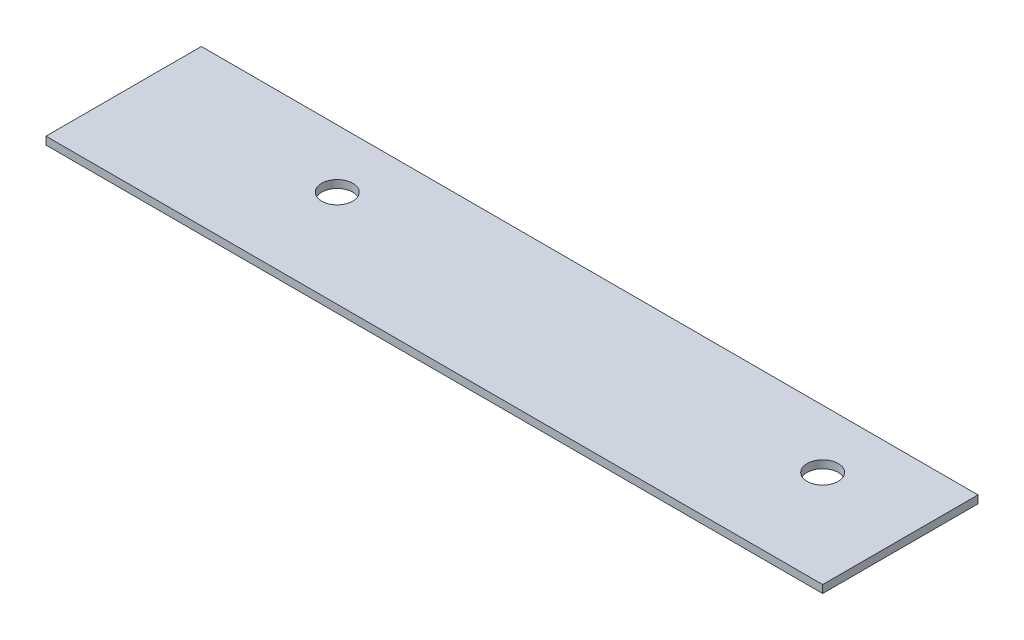
SolidWorks part; units mm, degrees
ref_plane "Front Plane" through (0, 0, 0) normal (0, 0, 1) x (1, 0, 0)
ref_plane "Top Plane" through (0, 0, 0) normal (0, 1, 0) x (1, 0, 0)
ref_plane "Right Plane" through (0, 0, 0) normal (1, 0, 0) x (0, 0, -1)
sketch "Sketch1" plane through (0, 0, 0) normal (0, 1, 0) x (1, 0, 0)
  line L1 (0, 0) -> (80, 0)
  line L2 (0, 0) -> (0, 16)
  line L3 (0, 16) -> (80, 16)
  line L4 (80, 0) -> (80, 16)
  circle A0 centre (20, 10) radius 1.6
  circle A1 centre (70, 10) radius 1.6
  point P8 (0, 0)
  dimension "D3" = 20
  dimension "D5" = 3.2
  dimension "D1" = 80
  dimension "D2" = 16
  dimension "D4" = 10
  dimension "D6" = 70
extrude "Boss-Extrude1" add sketch "Sketch1" along normal blind 0.8
